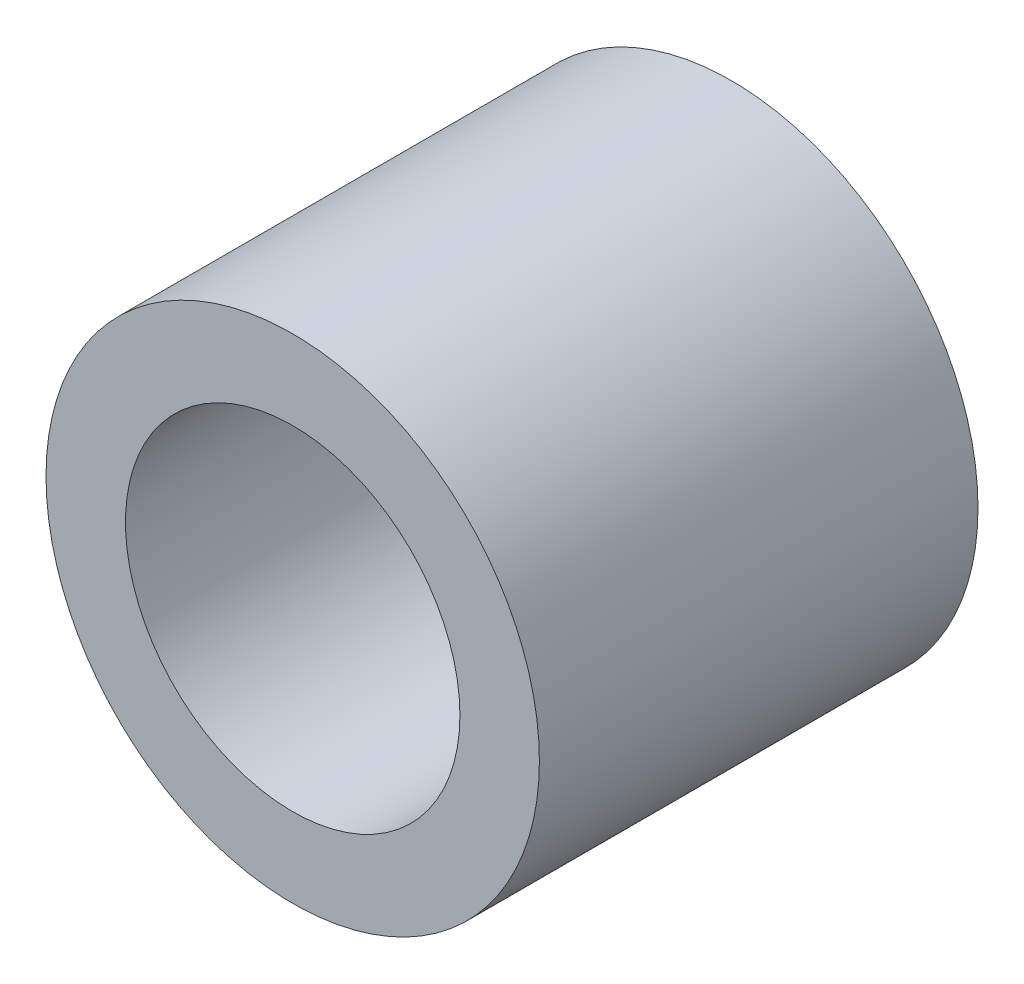
SolidWorks part; units mm, degrees
ref_plane "Front" through (0, 0, 0) normal (0, 0, 1) x (1, 0, 0)
ref_plane "Top" through (0, 0, 0) normal (0, 1, 0) x (1, 0, 0)
ref_plane "Right" through (0, 0, 0) normal (1, 0, 0) x (0, 0, -1)
sketch "草图1" plane through (0, 0, 0) normal (0, 0, 1) x (1, 0, 0)
  circle A0 centre (0, 0) radius 2.25
  dimension "D1" = 4.5
extrude "凸台-拉伸1" add sketch "草图1" along normal blind 1.5
sketch "草图3" plane through (0, 0, 1.5) normal (0, 0, 1) x (1, 0, 0)
  circle A0 centre (0, 0) radius 2.25
  dimension "D1" = 4.5
extrude "凸台-拉伸2" add sketch "草图3" along normal blind 2.5
sketch "草图4" plane through (0, 0, 1.5) normal (0, 0, 1) x (1, 0, 0)
  circle A0 centre (0, 0) radius 1.525
  dimension "D1" = 3.05
extrude "切除-拉伸1" cut sketch "草图4" along normal through all
